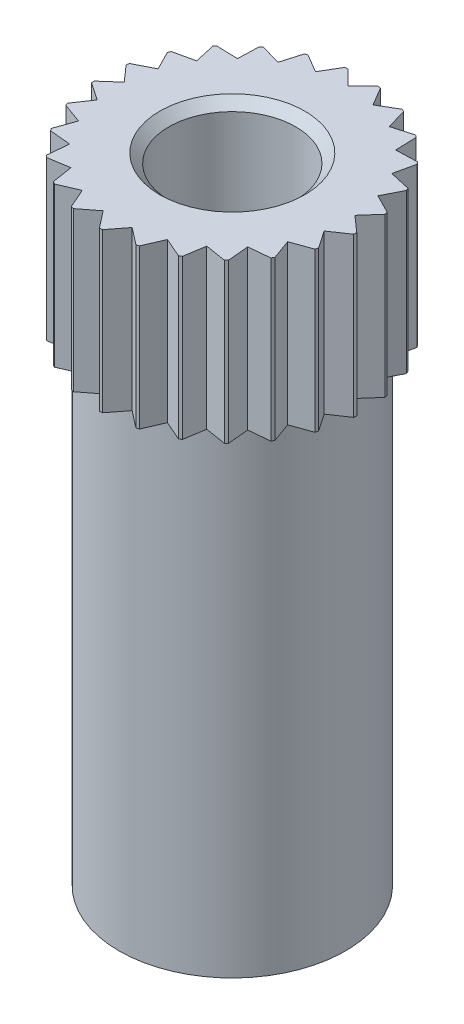
SolidWorks part; units mm, degrees
ref_plane "Front" through (0, 0, 0) normal (0, 0, 1) x (1, 0, 0)
ref_plane "Top" through (0, 0, 0) normal (0, 1, 0) x (1, 0, 0)
ref_plane "Right" through (0, 0, 0) normal (1, 0, 0) x (0, 0, -1)
sketch "Эскиз1" plane through (0, 0, 0) normal (0, 1, 0) x (1, 0, 0)
  circle A0 centre (0, 0) radius 2.9
  dimension "D1" = 5.8
extrude "Бобышка-Вытянуть1" add sketch "Эскиз1" along normal blind 3.5
sketch "Эскиз2" plane through (0, 0, 0) normal (0, -1, 0) x (1, 0, 0)
  circle A0 centre (0, 0) radius 2.5
  dimension "D1" = 5
extrude "Бобышка-Вытянуть2" add sketch "Эскиз2" along normal blind 10.5
sketch "Эскиз3" plane through (0, 3.5, 0) normal (0, 1, 0) x (1, 0, 0)
  line L0 (0, 2.55) -> (-0.3665, 2.9165)
  line L1 (-0.3665, 2.9165) -> (0.3665, 2.9165)
  line L2 (0.3665, 2.9165) -> (0, 2.55)
  line L3 (0.6342, 2.4699) -> (0.3703, 2.916)
  line L4 (0.3703, 2.916) -> (1.0803, 2.7337)
  line L5 (1.0803, 2.7337) -> (0.6342, 2.4699)
  line L6 (1.2285, 2.2346) -> (1.0839, 2.7323)
  line L7 (1.0839, 2.7323) -> (1.7262, 2.3792)
  line L8 (1.7262, 2.3792) -> (1.2285, 2.2346)
  line L9 (1.7456, 1.8589) -> (1.7293, 2.3769)
  line L10 (1.7293, 2.3769) -> (2.2636, 1.8752)
  line L11 (2.2636, 1.8752) -> (1.7456, 1.8589)
  line L12 (2.153, 1.3664) -> (2.2661, 1.8722)
  line L13 (2.2661, 1.8722) -> (2.6589, 1.2533)
  line L14 (2.6589, 1.2533) -> (2.153, 1.3664)
  line L15 (2.4252, 0.788) -> (2.6605, 1.2498)
  line L16 (2.6605, 1.2498) -> (2.887, 0.5527)
  line L17 (2.887, 0.5527) -> (2.4252, 0.788)
  line L18 (2.545, 0.1601) -> (2.8877, 0.5489)
  line L19 (2.8877, 0.5489) -> (2.9338, -0.1826)
  line L20 (2.9338, -0.1826) -> (2.545, 0.1601)
  line L21 (2.5048, -0.4778) -> (2.9335, -0.1865)
  line L22 (2.9335, -0.1865) -> (2.7962, -0.9065)
  line L23 (2.7962, -0.9065) -> (2.5048, -0.4778)
  line L24 (2.3073, -1.0857) -> (2.795, -0.9102)
  line L25 (2.795, -0.9102) -> (2.4829, -1.5734)
  line L26 (2.4829, -1.5734) -> (2.3073, -1.0857)
  line L27 (1.9648, -1.6254) -> (2.4808, -1.5767)
  line L28 (2.4808, -1.5767) -> (2.0136, -2.1414)
  line L29 (2.0136, -2.1414) -> (1.9648, -1.6254)
  line L30 (1.4989, -2.063) -> (2.0108, -2.1441)
  line L31 (2.0108, -2.1441) -> (1.4178, -2.5749)
  line L32 (1.4178, -2.5749) -> (1.4989, -2.063)
  line L33 (0.9387, -2.3709) -> (1.4144, -2.5768)
  line L34 (1.4144, -2.5768) -> (0.7329, -2.8466)
  line L35 (0.7329, -2.8466) -> (0.9387, -2.3709)
  line L36 (0.3196, -2.5299) -> (0.7291, -2.8476)
  line L37 (0.7291, -2.8476) -> (0.0019, -2.9394)
  line L38 (0.0019, -2.9394) -> (0.3196, -2.5299)
  line L39 (-0.3196, -2.5299) -> (-0.0019, -2.9394)
  line L40 (-0.0019, -2.9394) -> (-0.7291, -2.8476)
  line L41 (-0.7291, -2.8476) -> (-0.3196, -2.5299)
  line L42 (-0.9387, -2.3709) -> (-0.7329, -2.8466)
  line L43 (-0.7329, -2.8466) -> (-1.4144, -2.5768)
  line L44 (-1.4144, -2.5768) -> (-0.9387, -2.3709)
  line L45 (-1.4989, -2.063) -> (-1.4178, -2.5749)
  line L46 (-1.4178, -2.5749) -> (-2.0108, -2.1441)
  line L47 (-2.0108, -2.1441) -> (-1.4989, -2.063)
  line L48 (-1.9648, -1.6254) -> (-2.0136, -2.1414)
  line L49 (-2.0136, -2.1414) -> (-2.4808, -1.5767)
  line L50 (-2.4808, -1.5767) -> (-1.9648, -1.6254)
  line L51 (-2.3073, -1.0857) -> (-2.4829, -1.5734)
  line L52 (-2.4829, -1.5734) -> (-2.795, -0.9102)
  line L53 (-2.795, -0.9102) -> (-2.3073, -1.0857)
  line L54 (-2.5048, -0.4778) -> (-2.7962, -0.9065)
  line L55 (-2.7962, -0.9065) -> (-2.9335, -0.1865)
  line L56 (-2.9335, -0.1865) -> (-2.5048, -0.4778)
  line L57 (-2.545, 0.1601) -> (-2.9338, -0.1826)
  line L58 (-2.9338, -0.1826) -> (-2.8877, 0.5489)
  line L59 (-2.8877, 0.5489) -> (-2.545, 0.1601)
  line L60 (-2.4252, 0.788) -> (-2.887, 0.5527)
  line L61 (-2.887, 0.5527) -> (-2.6605, 1.2498)
  line L62 (-2.6605, 1.2498) -> (-2.4252, 0.788)
  line L63 (-2.153, 1.3664) -> (-2.6589, 1.2533)
  line L64 (-2.6589, 1.2533) -> (-2.2661, 1.8722)
  line L65 (-2.2661, 1.8722) -> (-2.153, 1.3664)
  line L66 (-1.7456, 1.8589) -> (-2.2636, 1.8752)
  line L67 (-2.2636, 1.8752) -> (-1.7293, 2.3769)
  line L68 (-1.7293, 2.3769) -> (-1.7456, 1.8589)
  line L69 (-1.2285, 2.2346) -> (-1.7262, 2.3792)
  line L70 (-1.7262, 2.3792) -> (-1.0839, 2.7323)
  line L71 (-1.0839, 2.7323) -> (-1.2285, 2.2346)
  line L72 (-0.6342, 2.4699) -> (-1.0803, 2.7337)
  line L73 (-1.0803, 2.7337) -> (-0.3703, 2.916)
  line L74 (-0.3703, 2.916) -> (-0.6342, 2.4699)
  circle A0 centre (0, 0) radius 2.55 construction
  point P81 (0, 0)
  dimension "D1" = 5.1
  dimension "D2" = 90
  dimension "D3" = 25
extrude "Вырез-Вытянуть1" cut sketch "Эскиз3" against normal blind 4
hole_wizard "Сверло под метчик  спиральное M32" positions "Эскиз8" profile "Эскиз7" hole size "M3x0.5" standard "Din"
sketch "Эскиз8" plane through (0, 3.5, 0) normal (0, 1, 0) x (1, 0, 0)
  point P0 (0, 0)
sketch "Эскиз7" plane through (0, 3.5, 0) normal (1, 0, 0) x (0, 0, 1)
  line L0 (0, 0) -> (0, 7.4)
  line L1 (0, 7.4) -> (1.4, 6)
  line L2 (1.4, 6) -> (1.4, 0.2)
  line L3 (1.4, 0.2) -> (1.6, 0)
  line L5 (1.6, 0) -> (0, 0)
  line L6 (-1.4, 0.2) -> (-1.6, 0) construction
  line L10 (0, 7.4) -> (-1.4, 6) construction
  line L11 (0, -6.35) -> (0, 107.95) construction
  dimension "Диаметр отверстия" = 2.8
  dimension "Глубина отверстия" = 6
  dimension "Диаметр передней зенковки" = 3.2
  dimension "Угол передней зенковки" = 90
  dimension "Угол заточки сверла" = 90
